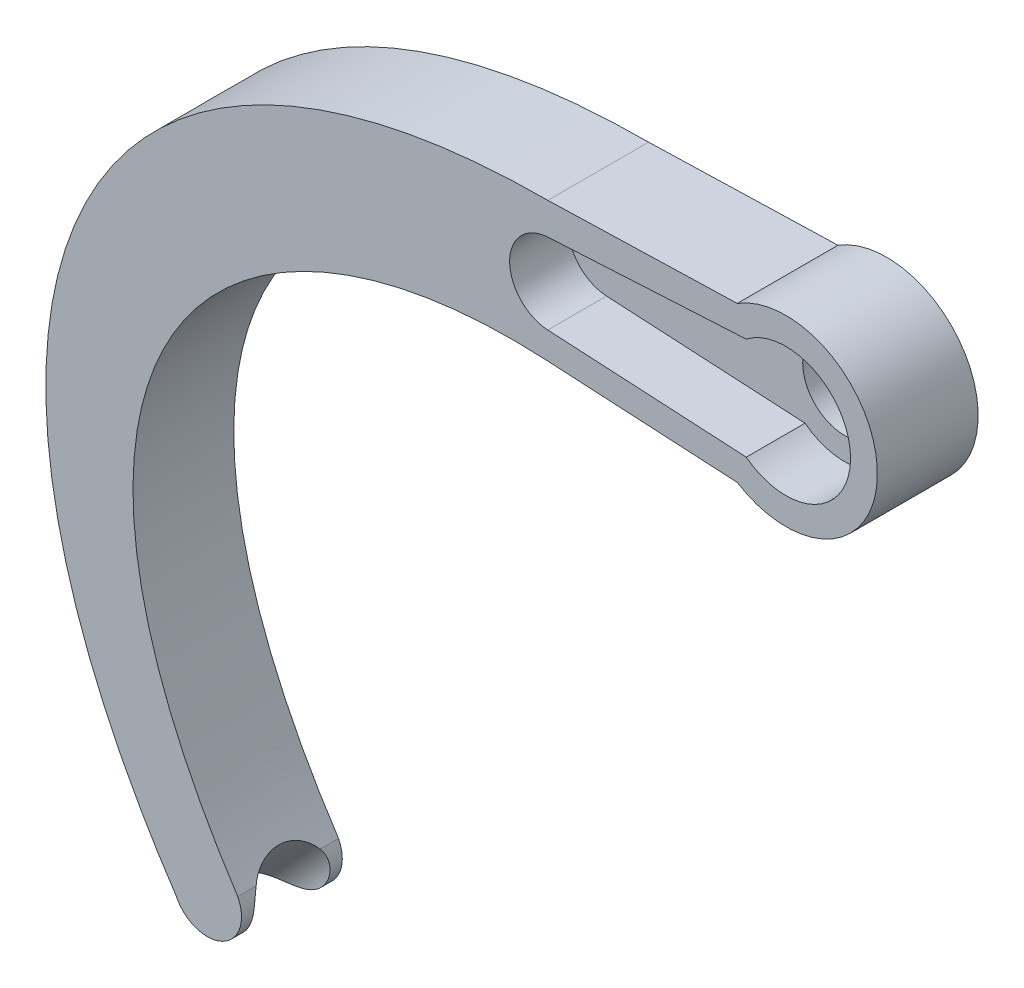
SolidWorks part; units mm, degrees
ref_plane "Front Plane" through (0, 0, 0) normal (0, 0, 1) x (1, 0, 0)
ref_plane "Top Plane" through (0, 0, 0) normal (0, 1, 0) x (1, 0, 0)
ref_plane "Right Plane" through (0, 0, 0) normal (1, 0, 0) x (0, 0, -1)
sketch "Sketch1" plane through (0, 0, 0) normal (0, 0, 1) x (1, 0, 0)
  line L0 (-14.2682, -3.994) -> (-34.7312, -2.8748) construction
  line L1 (-34.7312, -2.8748) -> (-47.0184, -18.9715) construction
  line L4 (0, 0) -> (0, 6)
  line L7 (-47.0184, -18.9715) -> (-32.6408, -40.8457) construction
  line L8 (-14.1753, 4.2925) -> (-42.4623, 4.2888) construction
  line L9 (-42.4623, 4.2888) -> (-52.5338, -18.3721) construction
  line L10 (-52.5338, -18.3721) -> (-36.3028, -42.6554) construction
  line L11 (-14.2095, -1.9943) -> (-2.2091, -2.65)
  line L12 (-2.2285, 2.6337) -> (-14.1644, 2.292)
  line L13 (-14.2682, -3.994) -> (-2.8985, -4.6153)
  line L14 (-2.8985, 4.6153) -> (-14.1753, 4.2925)
  arc A6 (-2.8985, -4.6153) -> (-2.8985, 4.6153) centre (0, 0) ccw
  arc A7 (-36.3028, -42.6554) -> (-32.6408, -40.8457) centre (-34.4578, -41.7789) ccw
  arc A8 (-14.1644, 2.292) -> (-14.2095, -1.9943) centre (-14.2218, 0.1492) ccw
  arc A9 (-2.2091, -2.65) -> (-2.2285, 2.6337) centre (0, 0) ccw
  arc A12 (-14.1753, 4.2925) -> (-14.2682, -3.994) centre (-14.2218, 0.1492) ccw construction
  spline S0 degree 3 poles (-14.2682, -3.994) (-34.7312, -2.8748) (-47.0184, -18.9715) (-32.6408, -40.8457) knots 0 0 0 0 1 1 1 1
  spline S1 degree 3 poles (-14.1753, 4.2925) (-42.4623, 4.2888) (-52.5338, -18.3721) (-36.3028, -42.6554) knots 0 0 0 0 1 1 1 1
  dimension "D1" = 6
  dimension "D2" = 2
extrude "Boss-Extrude1" add sketch "Sketch1" along normal blind 6 contours S1 A7 S0 L13 A6 L14
sketch "Sketch3" plane through (0, 0, 0) normal (0, 0, 1) x (1, 0, 0)
  line L9 (-14.1809, -2.3964) -> (-2.3593, -3.0424)
  line L10 (-2.3593, 3.0424) -> (-14.1809, 2.3964)
  arc A11 (-2.3593, -3.0424) -> (-2.3593, 3.0424) centre (0, 0) ccw
  arc A12 (-14.1809, 2.3964) -> (-14.1809, -2.3964) centre (-14.05, 0) ccw
extrude "Cut-Extrude1" cut sketch "Sketch3" along normal blind 3.5
sketch "Sketch4" plane through (0, 0, 3.5) normal (0, 0, -1) x (-1, 0, 0)
  circle A0 centre (0, 0) radius 2.5
  dimension "D1" = 5
extrude "Cut-Extrude2" cut sketch "Sketch4" against normal blind 3.5
ref_plane "Plane1" through (3.7258, 3.9776, 0) normal (0.6836, 0.7298, 0) x (0, 0, -1)
sketch "Sketch5" plane through (3.7258, 3.9776, 0) normal (0.6836, 0.7298, 0) x (0, 0, -1)
  line L0 (-6, -5.4554) -> (0, -5.4554) construction
  ellipse E0 centre (-3, -5.4554) end of major axis (-3, -7.8241) minor radius 2.322
ref_plane "Plane2" through (-23.6193, -25.2157, 0) normal (0.6836, 0.7298, 0) x (0, 0, -1)
sketch "Sketch6" plane through (-23.6193, -25.2157, 0) normal (0.6836, 0.7298, 0) x (0, 0, -1)
  ellipse E0 centre (-3, -5.4554) end of major axis (-3, -7.8241) minor radius 2.322 construction
  ellipse E1 centre (-3, -5.4554) end of major axis (-3, -7.8241) minor radius 2.322
extrude "Cut-Extrude3" cut sketch "Sketch6" against normal blind 30
ref_plane "Plane3" through (0, 0, -40) normal (0, 0, -1) x (-1, 0, 0)
mirror "Mirror3" about plane through (0, 0, -40) normal (0, 0, -1) of bodies 107
delete or keep bodies "Body-Delete/Keep 1" type delete bodies bodies 107
